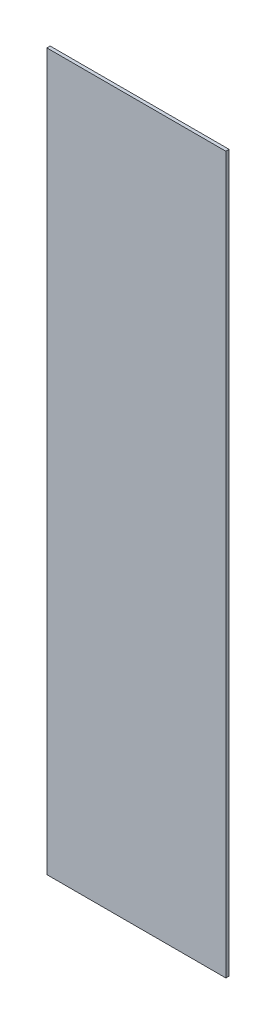
SolidWorks part; units mm, degrees
material "OSB_Plywood"
ref_plane "Front Plane" through (0, 0, 0) normal (0, 0, 1) x (1, 0, 0)
ref_plane "Top Plane" through (0, 0, 0) normal (0, 1, 0) x (1, 0, 0)
ref_plane "Right Plane" through (0, 0, 0) normal (1, 0, 0) x (0, 0, -1)
sketch "Sketch1" plane through (0, 0, 0) normal (0, 0, 1) x (1, 0, 0)
  line L1 (0, 0) -> (609.6, 0)
  line L2 (0, 0) -> (0, 2438.4)
  line L3 (0, 2438.4) -> (609.6, 2438.4)
  line L4 (609.6, 0) -> (609.6, 2438.4)
  dimension "D1" = 609.6
  dimension "D2" = 2438.4
extrude "Boss-Extrude1" add sketch "Sketch1" along normal blind 11.1125
